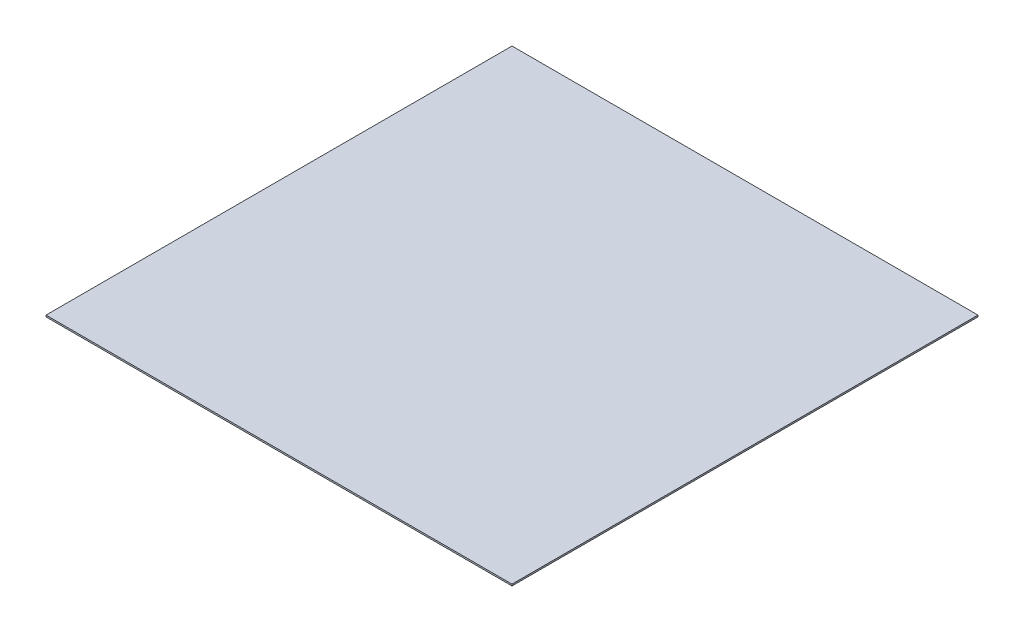
SolidWorks part; units mm, degrees
ref_plane "Front Plane" through (0, 0, 0) normal (0, 0, 1) x (1, 0, 0)
ref_plane "Top Plane" through (0, 0, 0) normal (0, 1, 0) x (1, 0, 0)
ref_plane "Right Plane" through (0, 0, 0) normal (1, 0, 0) x (0, 0, -1)
sketch "Sketch1" plane through (0, 0, 0) normal (0, 1, 0) x (1, 0, 0)
  line L1 (435, -435) -> (-435, -435)
  line L2 (435, -435) -> (435, 435)
  line L3 (435, 435) -> (-435, 435)
  line L4 (-435, -435) -> (-435, 435)
  line L5 (435, -435) -> (-435, 435) construction
  line L6 (435, 435) -> (-435, -435) construction
  point P0 (0, 0)
  dimension "D1" = 870
  dimension "D2" = 870
extrude "Boss-Extrude1" add sketch "Sketch1" along normal blind 3
sketch "Sketch3" plane through (0, 3, 0) normal (0, 1, 0) x (1, 0, 0)
  line L8 (-435, 335) -> (-435, 285)
  line L9 (-435, 435) -> (285, 435)
  line L10 (-435, 435) -> (-435, 385)
  line L11 (-435, 385) -> (285, 385)
  line L12 (285, 435) -> (285, 385)
  line L13 (-435, 385) -> (285, 385)
  line L14 (-435, 385) -> (-435, 335)
  line L15 (-435, 335) -> (285, 335)
  line L16 (285, 385) -> (285, 335)
  line L17 (-435, 335) -> (285, 335)
  line L18 (285, 335) -> (285, 285)
  line L19 (-435, 285) -> (285, 285)
  line L20 (-435, 285) -> (-435, 235)
  line L21 (-435, 285) -> (285, 285)
  line L22 (285, 285) -> (285, 235)
  line L23 (-435, 235) -> (285, 235)
  line L24 (-435, 235) -> (-435, 185)
  line L25 (-435, 235) -> (285, 235)
  line L26 (285, 235) -> (285, 185)
  line L27 (-435, 185) -> (285, 185)
  line L28 (-435, 185) -> (-435, 135)
  line L29 (-435, 185) -> (285, 185)
  line L30 (285, 185) -> (285, 135)
  line L31 (-435, 135) -> (285, 135)
  line L32 (-435, 135) -> (-435, 85)
  line L33 (-435, 135) -> (285, 135)
  line L34 (285, 135) -> (285, 85)
  line L35 (-435, 85) -> (285, 85)
  line L36 (-435, 85) -> (-435, 35)
  line L37 (-435, 85) -> (285, 85)
  line L38 (285, 85) -> (285, 35)
  line L39 (-435, 35) -> (285, 35)
  line L40 (-435, 35) -> (-435, -15)
  line L41 (-435, 35) -> (285, 35)
  line L42 (285, 35) -> (285, -15)
  line L43 (-435, -15) -> (285, -15)
  line L44 (-435, -15) -> (-435, -65)
  line L45 (-435, -15) -> (285, -15)
  line L46 (285, -15) -> (285, -65)
  line L47 (-435, -65) -> (285, -65)
  line L48 (-435, -65) -> (-435, -115)
  line L49 (-435, -65) -> (285, -65)
  line L50 (285, -65) -> (285, -115)
  line L51 (-435, -115) -> (285, -115)
  line L52 (-435, -115) -> (-435, -165)
  line L53 (-435, -115) -> (285, -115)
  line L54 (285, -115) -> (285, -165)
  line L55 (-435, -165) -> (285, -165)
  line L56 (-435, -165) -> (-435, -215)
  line L57 (-435, -165) -> (285, -165)
  line L58 (285, -165) -> (285, -215)
  line L59 (-435, -215) -> (285, -215)
  line L60 (-435, -215) -> (-435, -265)
  line L61 (-435, -215) -> (285, -215)
  line L62 (285, -215) -> (285, -265)
  line L63 (-435, -265) -> (285, -265)
  line L64 (-435, -265) -> (-435, -315)
  line L65 (-435, -265) -> (285, -265)
  line L66 (285, -265) -> (285, -315)
  line L67 (-435, -315) -> (285, -315)
  line L68 (-435, -315) -> (-435, -365)
  line L69 (-435, -315) -> (285, -315)
  line L70 (285, -315) -> (285, -365)
  line L71 (-435, -365) -> (285, -365)
  line L72 (-255, 285) -> (-255, -365)
  line L73 (-75, 285) -> (-75, -365)
  line L74 (105, 285) -> (105, -365)
  line L76 (285, 435) -> (335, 435)
  line L77 (285, 435) -> (285, 255)
  line L78 (285, 255) -> (335, 255)
  line L79 (335, 435) -> (335, 255)
  line L80 (285, 255) -> (335, 255)
  line L81 (285, 255) -> (285, 75)
  line L82 (285, 75) -> (335, 75)
  line L83 (335, 255) -> (335, 75)
  line L84 (285, 75) -> (335, 75)
  line L85 (285, 75) -> (285, -105)
  line L86 (285, -105) -> (335, -105)
  line L87 (335, 75) -> (335, -105)
  line L88 (285, -105) -> (335, -105)
  line L89 (285, -105) -> (285, -285)
  line L90 (285, -285) -> (335, -285)
  line L91 (335, -105) -> (335, -285)
  point P7 (-75, -340)
  point P13 (-75, -390)
  point P18 (-75, -440)
  point P23 (-75, -490)
  point P28 (-75, -540)
  point P33 (-75, -590)
  point P38 (-75, -640)
  point P43 (-75, -690)
  point P48 (-75, -740)
  point P53 (-75, -790)
  point P58 (-75, -840)
  point P63 (-75, -890)
  point P68 (-75, -940)
  point P73 (-75, -990)
  point P78 (-75, -1040)
  dimension "D1" = 720
  dimension "D2" = 50
  dimension "D3" = 50
  dimension "D4" = 15
  dimension "D5" = 50
  dimension "D6" = 180
  dimension "D7" = 180
  dimension "D8" = 180
  dimension "D9" = 50
  dimension "D10" = 180
  dimension "D11" = 180
  dimension "D12" = 180
